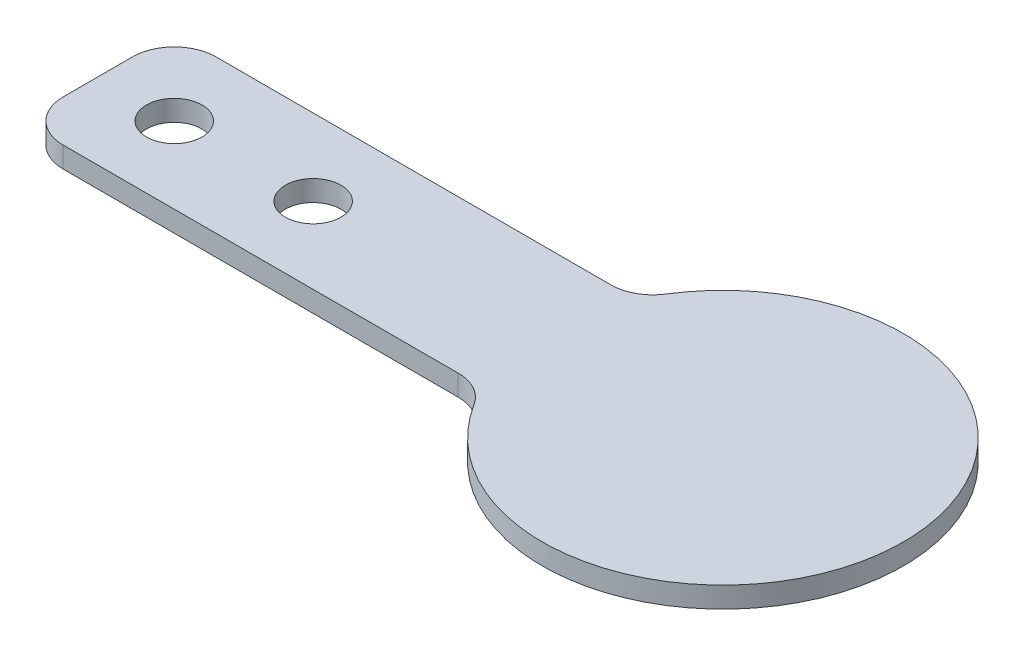
SolidWorks part; units mm, degrees
ref_plane "Front" through (0, 0, 0) normal (0, 0, 1) x (1, 0, 0)
ref_plane "Top" through (0, 0, 0) normal (0, 1, 0) x (1, 0, 0)
ref_plane "Right" through (0, 0, 0) normal (1, 0, 0) x (0, 0, -1)
sketch "Эскиз1" plane through (0, 0, 0) normal (0, 1, 0) x (1, 0, 0)
  line L0 (5.5, -5.5) -> (0, -5.5) construction
  line L1 (3, 0) -> (31.4446, 0)
  line L2 (0, -3) -> (0, -8)
  line L3 (3, -11) -> (31.4446, -11)
  line L5 (15.5, -5.5) -> (5.5, -5.5) construction
  line L6 (5.5, -5.5) -> (5.5, 0) construction
  circle A0 centre (5.5, -5.5) radius 2
  circle A1 centre (15.5, -5.5) radius 2
  arc A2 (33.9862, -12.4062) -> (33.9862, 1.4063) centre (45, -5.5) ccw
  arc A3 (0, -8) -> (3, -11) centre (3, -8) ccw
  arc A4 (3, 0) -> (0, -3) centre (3, -3) ccw
  arc A5 (31.4446, 0) -> (33.9862, 1.4063) centre (31.4446, 3) ccw
  arc A6 (31.4446, -11) -> (33.9862, -12.4062) centre (31.4446, -14) cw
  point P14 (0, -11)
  point P17 (0, 0)
  dimension "D3" = 4
  dimension "D4" = 13
  dimension "D6" = 3
  dimension "D7" = 3
  dimension "D1" = 11
  dimension "D2" = 10
  dimension "D5" = 45
extrude "Бобышка-Вытянуть1" add sketch "Эскиз1" along normal blind 1.5
